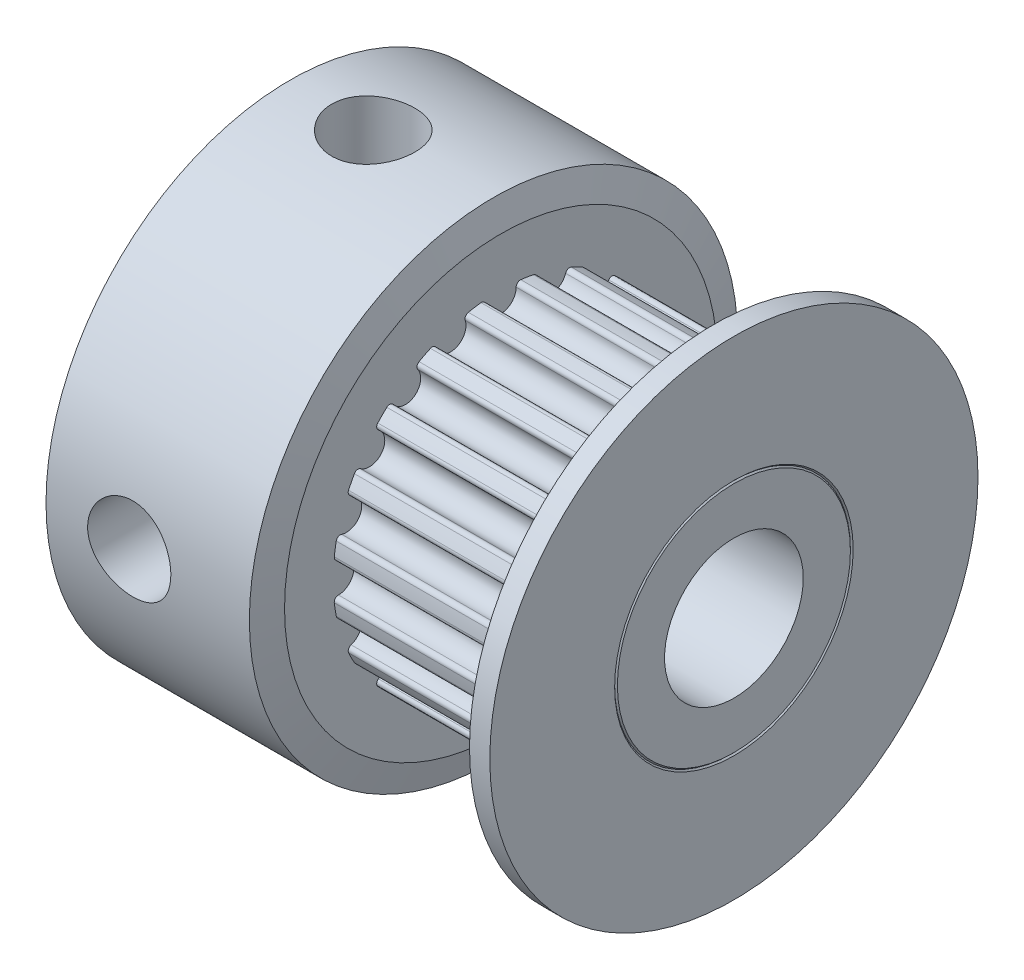
SolidWorks part; units mm, degrees
material "6063-T1"
ref_plane "Front Plane" through (0, 0, 0) normal (0, 0, 1) x (1, 0, 0)
ref_plane "Top Plane" through (0, 0, 0) normal (0, 1, 0) x (1, 0, 0)
ref_plane "Right Plane" through (0, 0, 0) normal (1, 0, 0) x (0, 0, -1)
sketch "Sketch1" plane through (0, 0, 0) normal (0, 0, 1) x (1, 0, 0)
  line L0 (0, 0) -> (0, 8.8)
  line L1 (0, 8.8) -> (6.6, 8.8)
  line L2 (6.6, 8.8) -> (7.3321, 8.8)
  line L3 (7.3321, 8.8) -> (7.6, 7.8)
  line L4 (7.6, 6.05) -> (15, 6.05)
  line L5 (15, 6.05) -> (15, 7.8)
  line L6 (15.2679, 8.8) -> (16, 8.8)
  line L7 (16, 0) -> (16, 4.2)
  line L8 (16, 4.3) -> (15.95, 4.25)
  line L9 (15.95, 4.25) -> (16, 4.2)
  line L10 (16, 4.3) -> (16, 8.8)
  line L11 (0, 0) -> (16, 0)
  line L12 (7.6, 7.8) -> (7.6, 6.05)
  line L13 (15, 7.8) -> (15.2679, 8.8)
  line L14 (0, 0) -> (-50000, 0) construction
  dimension "D2" = 0.05
  dimension "D3" = 15
  dimension "D4" = 4.25
  dimension "D5" = 1
  dimension "D6" = 6.05
  dimension "D7" = 17.6
  dimension "D9" = 1
  dimension "D10" = 9.4
revolve "Body" add sketch "Sketch1" angle 360 about L11
sketch "Sketch 2" plane through (16, 0, 0) normal (1, 0, 0) x (0, 0, -1)
  circle A0 centre (0, 0) radius 2.5
  dimension "D1" = 5
extrude "Bore" cut sketch "Sketch 2" against normal through all
sketch "Sketch 3" plane through (7.6, 0, 0) normal (1, 0, 0) x (0, 0, -1)
  line L0 (0, 0) -> (9.7637, 0) construction
  circle A0 centre (5.5684, -1.8093) radius 0.55
  circle A2 centre (4.7368, -3.4415) radius 0.55
  circle A3 centre (3.4415, -4.7368) radius 0.55
  circle A4 centre (1.8093, -5.5684) radius 0.55
  circle A5 centre (0, -5.855) radius 0.55
  circle A6 centre (5.855, 0) radius 0.55
  circle A7 centre (-1.8093, -5.5684) radius 0.55
  circle A8 centre (-3.4415, -4.7368) radius 0.55
  circle A9 centre (-4.7368, -3.4415) radius 0.55
  circle A10 centre (-5.5684, -1.8093) radius 0.55
  circle A11 centre (-5.855, 0) radius 0.55
  circle A12 centre (-5.5684, 1.8093) radius 0.55
  circle A13 centre (-4.7368, 3.4415) radius 0.55
  circle A14 centre (-3.4415, 4.7368) radius 0.55
  circle A17 centre (-1.8093, 5.5684) radius 0.55
  circle A18 centre (0, 5.855) radius 0.55
  circle A19 centre (1.8093, 5.5684) radius 0.55
  circle A20 centre (3.4415, 4.7368) radius 0.55
  circle A21 centre (4.7368, 3.4415) radius 0.55
  circle A22 centre (5.5684, 1.8093) radius 0.55
  point P45 (0, 0)
  dimension "D1" = 5.855
extrude "20tooth" cut sketch "Sketch 3" along normal up to surface (7.4 mm away) up to face at (15, 0, 7.8)
fillet "Filets" radius 0.15 40 edges at (11.3, 0.5223, -6.0274) (11.3, -0.5223, -6.0274) (11.3, -1.3659, -5.8938) (11.3, -2.3593, -5.571) (11.3, -3.1203, -5.1833) (11.3, -3.9654, -4.5693) (11.3, -4.5693, -3.9654) (11.3, -5.1833, -3.1203) (11.3, -5.571, -2.3593) (11.3, -5.8938, -1.3659) (11.3, -6.0274, -0.5223) (11.3, -6.0274, 0.5223) (11.3, -5.8938, 1.3659) (11.3, -5.571, 2.3593) (11.3, -5.1833, 3.1203) (11.3, -4.5693, 3.9654) (11.3, -3.9654, 4.5693) (11.3, -3.1203, 5.1833) (11.3, -2.3593, 5.571) (11.3, -1.3659, 5.8938) (11.3, -0.5223, 6.0274) (11.3, 0.5223, 6.0274) (11.3, 1.3659, 5.8938) (11.3, 2.3593, 5.571) (11.3, 3.1203, 5.1833) (11.3, 3.9654, 4.5693) (11.3, 4.5693, 3.9654) (11.3, 5.1833, 3.1203) (11.3, 5.571, 2.3593) (11.3, 5.8938, 1.3659) (11.3, 6.0274, 0.5223) (11.3, 6.0274, -0.5223) (11.3, 5.8938, -1.3659) (11.3, 5.571, -2.3593) (11.3, 5.1833, -3.1203) (11.3, 4.5693, -3.9654) (11.3, 3.9654, -4.5693) (11.3, 3.1203, -5.1833) (11.3, 2.3593, -5.571) (11.3, 1.3659, -5.8938)
sketch "Sketch 4" plane through (0, 0, 0) normal (0, 0, 1) x (1, 0, 0)
  circle A0 centre (3, 0) radius 1.5
  dimension "D1" = 3
  dimension "D2" = 3
extrude "Set screw" cut sketch "Sketch 4" along normal through all
ref_axis "Axis 1" through (0, 0, 0) along (1, 0, 0)
pattern_circular "Set screw pattern" count 2 over 270 about axis through (0, 0, 0) along (1, 0, 0) of "Set screw"
sketch "Sketch2" plane through (7.6, 0, 0) normal (1, 0, 0) x (0, 0, -1)
  circle A0 centre (0, 0) radius 5.725
  circle A2 centre (0, 0) radius 7.025
  dimension "D1" = 11.45
  dimension "D3" = 14.05
